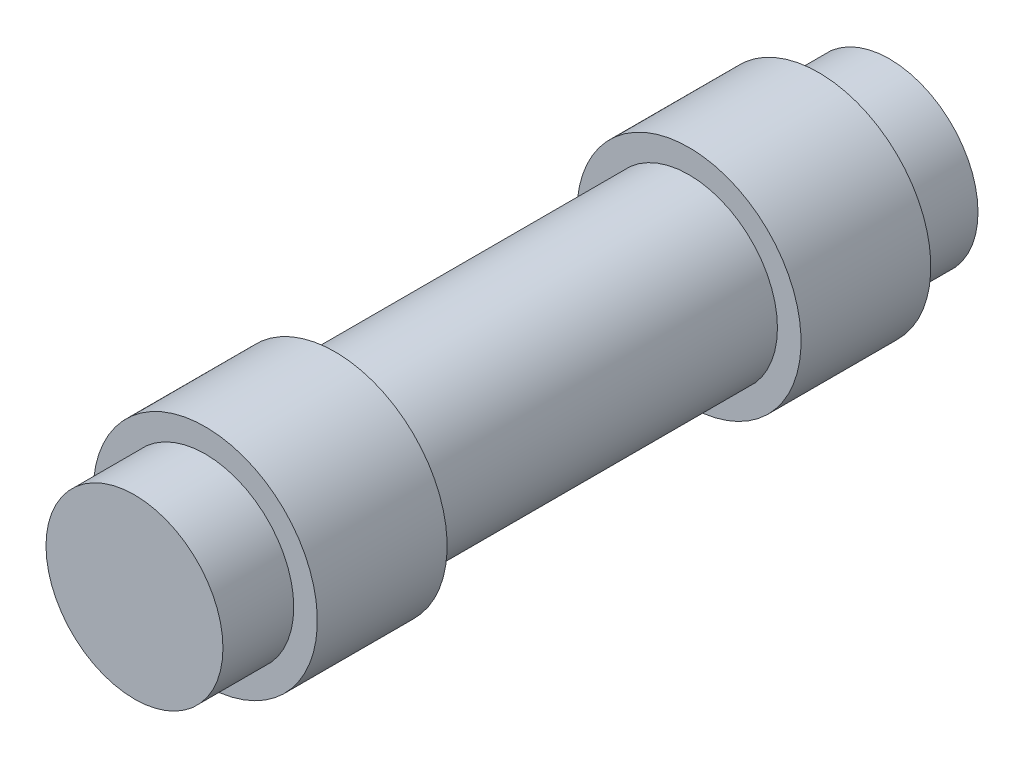
SolidWorks part; units mm, degrees
ref_plane "Front Plane" through (0, 0, 0) normal (0, 0, 1) x (1, 0, 0)
ref_plane "Top Plane" through (0, 0, 0) normal (0, 1, 0) x (1, 0, 0)
ref_plane "Right Plane" through (0, 0, 0) normal (1, 0, 0) x (0, 0, -1)
sketch "Sketch1" plane through (0, 0, 0) normal (0, 0, 1) x (1, 0, 0)
  circle A0 centre (0, 0) radius 3.75
  dimension "D1" = 7.5
extrude "Boss-Extrude1" add sketch "Sketch1" along normal blind 32
sketch "Sketch2" plane through (0, 0, 0) normal (0, 1, 0) x (1, 0, 0)
  line L0 (0, 0) -> (0, -32)
  line L1 (-3.75, -32) -> (3.75, -32) construction
  line L2 (0, -32) -> (3.75, -32)
  line L3 (3.75, -32) -> (3.75, 0)
  line L4 (3.75, 0) -> (0, 0)
  line L6 (3.75, -3) -> (4.75, -3)
  line L7 (3.75, -3) -> (3.75, -8.5)
  line L8 (3.75, -8.5) -> (4.75, -8.5)
  line L9 (4.75, -3) -> (4.75, -8.5)
  line L10 (3.75, -29) -> (4.75, -29)
  line L11 (3.75, -29) -> (3.75, -23.5)
  line L12 (3.75, -23.5) -> (4.75, -23.5)
  line L13 (4.75, -29) -> (4.75, -23.5)
  point P17 (4.25, -8.5)
  dimension "D1" = 1
  dimension "D2" = 1
  dimension "D3" = 15
  dimension "D4" = 5.5
  dimension "D5" = 5.5
  dimension "D6" = 3
revolve "Revolve1" add sketch "Sketch2" angle 360 about L0
